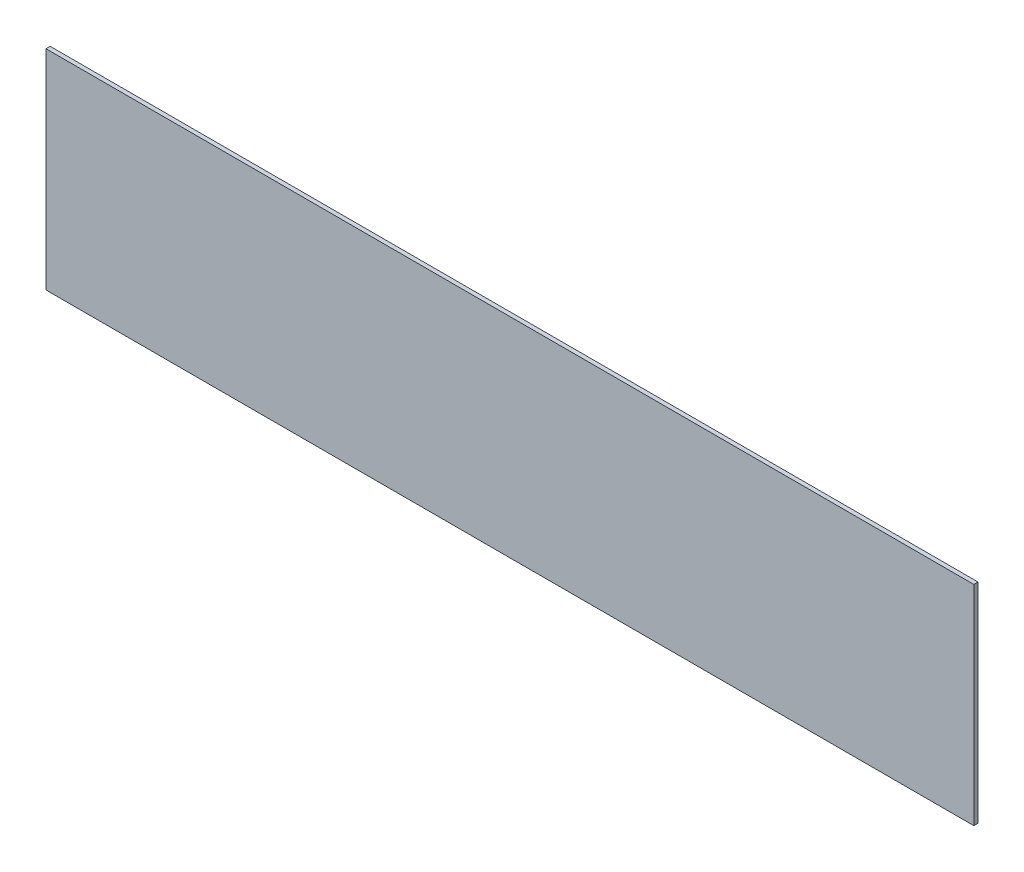
SolidWorks part; units mm, degrees
ref_plane "Front Plane" through (0, 0, 0) normal (0, 0, 1) x (1, 0, 0)
ref_plane "Top Plane" through (0, 0, 0) normal (0, 1, 0) x (1, 0, 0)
ref_plane "Right Plane" through (0, 0, 0) normal (1, 0, 0) x (0, 0, -1)
sketch "Sketch1" plane through (0, 0, 0) normal (0, 0, 1) x (1, 0, 0)
  line L1 (-56.2268, 43.6378) -> (165.7732, 43.6378)
  line L2 (-56.2268, 43.6378) -> (-56.2268, -6.3622)
  line L3 (-56.2268, -6.3622) -> (165.7732, -6.3622)
  line L4 (165.7732, 43.6378) -> (165.7732, -6.3622)
  dimension "D1" = 50
  dimension "D2" = 222
extrude "Boss-Extrude1" add sketch "Sketch1" along normal blind 1
